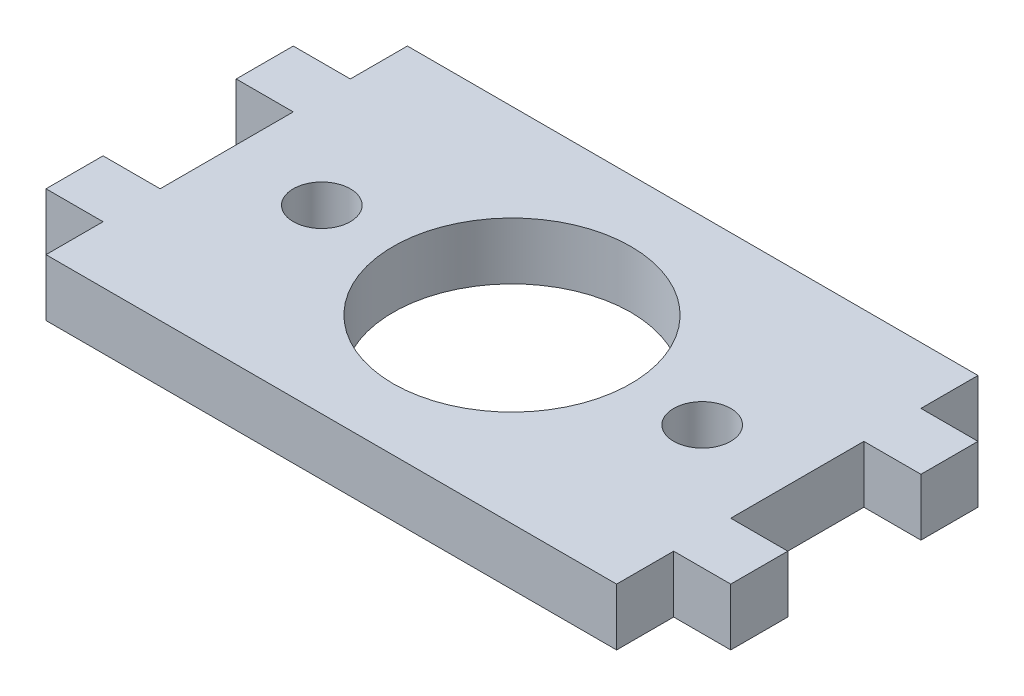
SolidWorks part; units mm, degrees
ref_plane "Front Plane" through (0, 0, 0) normal (0, 0, 1) x (1, 0, 0)
ref_plane "Top Plane" through (0, 0, 0) normal (0, 1, 0) x (1, 0, 0)
ref_plane "Right Plane" through (0, 0, 0) normal (1, 0, 0) x (0, 0, -1)
sketch "Sketch1" plane through (0, 0, 0) normal (0, 1, 0) x (1, 0, 0)
  line L0 (-42.8674, 7) -> (-42.8674, 10)
  line L1 (-42.8674, 10) -> (-39.8674, 10)
  line L2 (-39.8674, 10) -> (-39.8674, 13)
  line L3 (-39.8674, 13) -> (-9.8674, 13)
  line L4 (-9.8674, 13) -> (-9.8674, 10)
  line L5 (-9.8674, 10) -> (-6.8674, 10)
  line L6 (-6.8674, 10) -> (-6.8674, 7)
  line L7 (-6.8674, 7) -> (-9.8674, 7)
  line L8 (-9.8674, 7) -> (-9.8674, 0)
  line L9 (-9.8674, 0) -> (-6.8674, 0)
  line L10 (-6.8674, 0) -> (-6.8674, -3)
  line L11 (-6.8674, -3) -> (-9.8674, -3)
  line L12 (-9.8674, -3) -> (-9.8674, -6)
  line L13 (-9.8674, -6) -> (-39.8674, -6)
  line L14 (-39.8674, -6) -> (-39.8674, -3)
  line L15 (-39.8674, -3) -> (-42.8674, -3)
  line L16 (-42.8674, -3) -> (-42.8674, 0)
  line L17 (-42.8674, 0) -> (-39.8674, 0)
  line L18 (-39.8674, 0) -> (-39.8674, 7)
  line L19 (-39.8674, 7) -> (-42.8674, 7)
  line L20 (-24.8674, 13) -> (-24.8674, 3.5) construction
  line L21 (-24.8674, 3.5) -> (-34.8674, 3.5) construction
  circle A0 centre (-24.8674, 3.5) radius 6.25
  circle A1 centre (-34.8674, 3.5) radius 1.5
  circle A2 centre (-14.8674, 3.5) radius 1.5
  dimension "D6" = 12.5
  dimension "D7" = 3
  dimension "D1" = 3
  dimension "D2" = 3
  dimension "D3" = 30
  dimension "D4" = 7
  dimension "D5" = 3
extrude "Boss-Extrude1" add sketch "Sketch1" along normal blind 3
